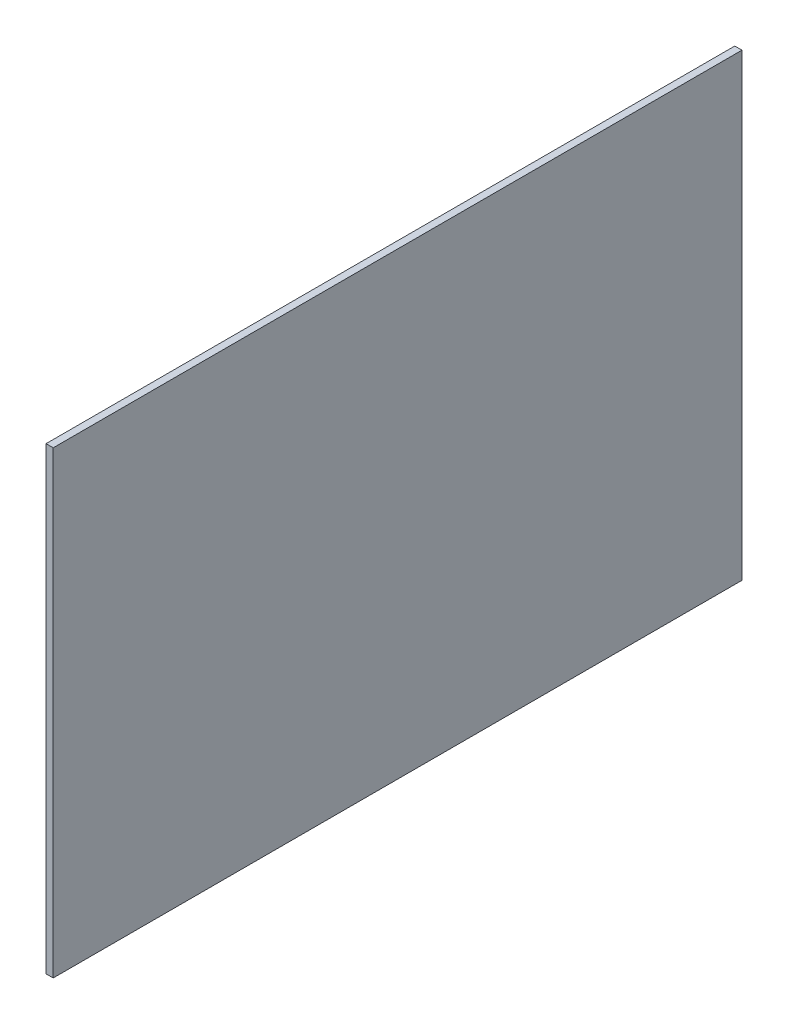
SolidWorks part; units mm, degrees
ref_plane "Front Plane" through (0, 0, 0) normal (0, 0, 1) x (1, 0, 0)
ref_plane "Top Plane" through (0, 0, 0) normal (0, 1, 0) x (1, 0, 0)
ref_plane "Right Plane" through (0, 0, 0) normal (1, 0, 0) x (0, 0, -1)
sketch "Sketch1" plane through (0, 0, 0) normal (1, 0, 0) x (0, 0, -1)
  line L1 (0, 0) -> (76.2, 0)
  line L2 (0, 0) -> (0, 50.8)
  line L3 (0, 50.8) -> (76.2, 50.8)
  line L4 (76.2, 0) -> (76.2, 50.8)
  dimension "D1" = 50.8
  dimension "D2" = 76.2
extrude "Boss-Extrude1" add sketch "Sketch1" along normal blind 0.7937
